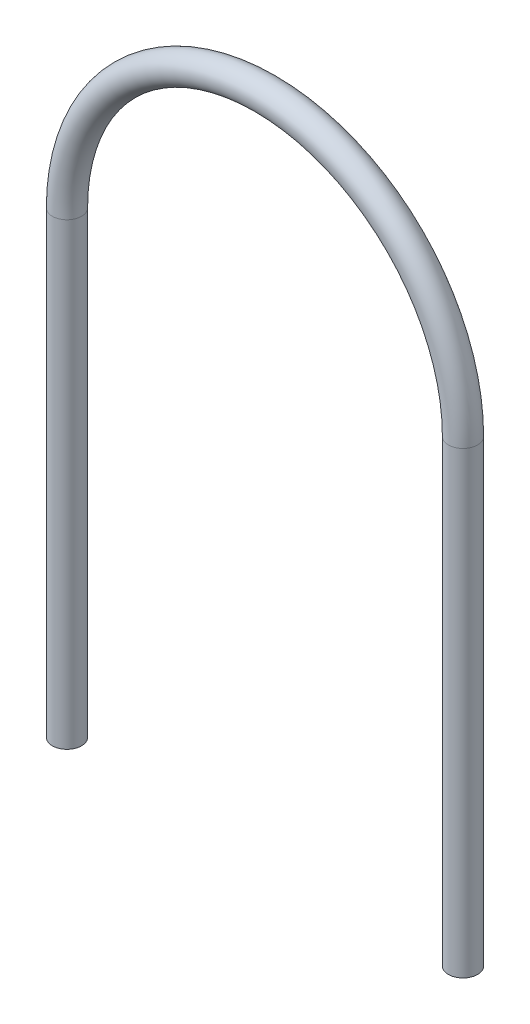
SolidWorks part; units mm, degrees
ref_plane "Front Plane" through (0, 0, 0) normal (0, 0, 1) x (1, 0, 0)
ref_plane "Top Plane" through (0, 0, 0) normal (0, 1, 0) x (1, 0, 0)
ref_plane "Right Plane" through (0, 0, 0) normal (1, 0, 0) x (0, 0, -1)
sketch "Sketch1" plane through (0, 0, 0) normal (0, 0, 1) x (1, 0, 0)
  line L0 (0, 0) -> (0, 63.5)
  line L2 (54.8386, 63.5) -> (54.8386, 0)
  arc A0 (0, 63.5) -> (54.8386, 63.5) centre (27.4193, 63.5) cw
  point P6 (49.1744, 103.6763)
  point P7 (0, 0)
  point P8 (0, 0)
  dimension "D2" = 63.5
  dimension "D1" = 54.8386
sketch "Sketch2" plane through (0, 0, 0) normal (0, 1, 0) x (1, 0, 0)
  circle A0 centre (0, 0) radius 2.0193
  dimension "D1" = 4.0386
sweep "Sweep3" add profiles "Sketch2" path "Sketch1"
